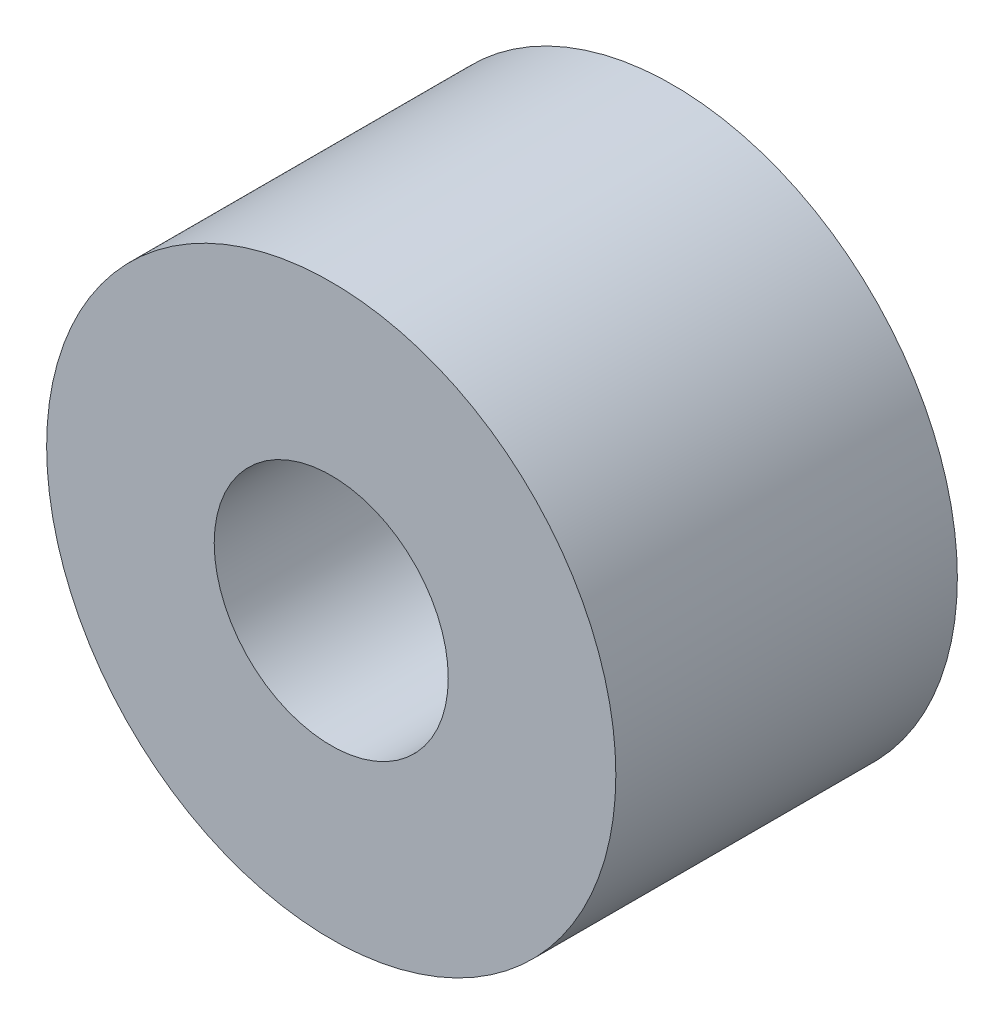
SolidWorks part; units mm, degrees
material "Delrin 2700 NC010, Low Viscosity Acetal Copolymer (SS)"
ref_plane "Front Plane" through (0, 0, 0) normal (0, 0, 1) x (1, 0, 0)
ref_plane "Top Plane" through (0, 0, 0) normal (0, 1, 0) x (1, 0, 0)
ref_plane "Right Plane" through (0, 0, 0) normal (1, 0, 0) x (0, 0, -1)
sketch "Sketch1" plane through (0, 0, 0) normal (0, 0, 1) x (1, 0, 0)
  circle A0 centre (0, 0) radius 7.9375
  dimension "D1" = 15.875
extrude "Boss-Extrude1" add sketch "Sketch1" along normal blind 9.525
hole_wizard "1/4 Clearance Hole1" positions "Sketch2" profile "Sketch3" hole size "1/4" standard "ANSI Inch" end condition through all
sketch "Sketch2" plane through (0, 0, 9.525) normal (0, 0, 1) x (1, 0, 0)
  point P0 (0, 0)
sketch "Sketch3" plane through (0, 0, 9.525) normal (1, 0, 0) x (0, -1, 0)
  line L0 (0, 0) -> (0, 9.525)
  line L1 (0, 9.525) -> (3.2639, 9.525)
  line L2 (3.2639, 9.525) -> (3.2639, 0)
  line L5 (3.2639, 0) -> (0, 0)
  line L11 (0, -6.35) -> (0, 107.95) construction
  dimension "Thru Hole Dia." = 6.5278
  dimension "Thru Hole Depth" = 9.525
